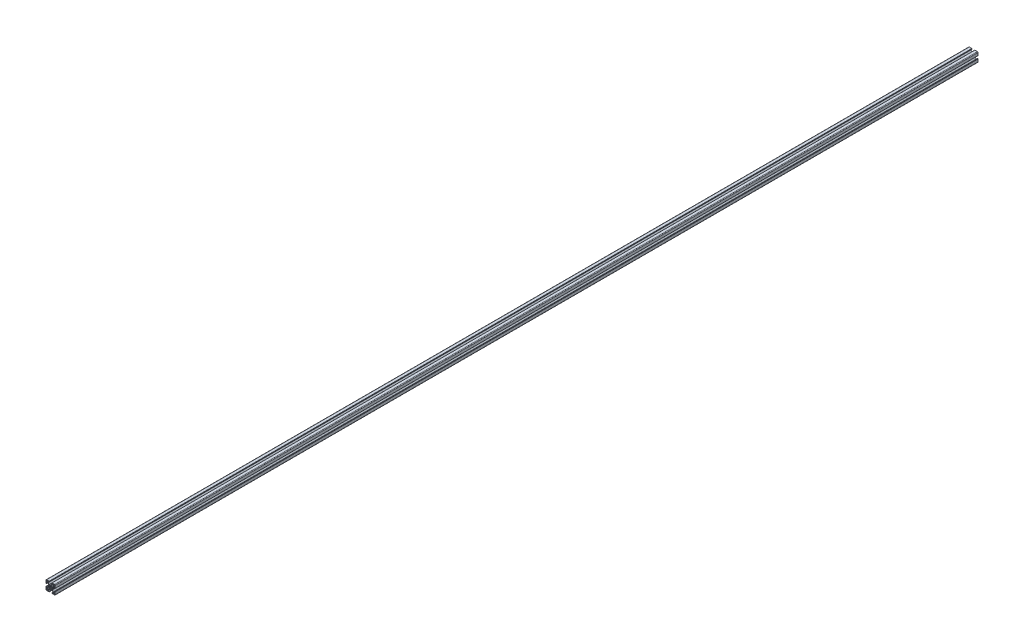
SolidWorks part; units mm, degrees
ref_plane "Płaszczyzna przednia" through (0, 0, 0) normal (0, 0, 1) x (1, 0, 0)
ref_plane "Płaszczyzna górna" through (0, 0, 0) normal (0, 1, 0) x (1, 0, 0)
ref_plane "Płaszczyzna prawa" through (0, 0, 0) normal (1, 0, 0) x (0, 0, -1)
sketch "Sketch1" plane through (0, 0, 0) normal (0, 0, 1) x (1, 0, 0)
  line L0 (109.26, 48.76) -> (107.06, 48.76)
  line L1 (106.06, 47.76) -> (106.06, 45.56)
  line L2 (107.06, 44.56) -> (109.26, 44.56)
  line L3 (110.26, 45.56) -> (110.26, 47.76)
  line L4 (94.9599, 38.3406) -> (93.4241, 39.5784)
  line L5 (92.0547, 38.2147) -> (93.2794, 36.6601)
  line L6 (93.2794, 33.4599) -> (92.0547, 31.9053)
  line L7 (93.4241, 30.5416) -> (94.9599, 31.7794)
  line L8 (98.1601, 31.7794) -> (99.6959, 30.5416)
  line L9 (101.0653, 31.9053) -> (99.8406, 33.4599)
  line L10 (99.8406, 36.6601) -> (101.0653, 38.2147)
  line L11 (99.6959, 39.5784) -> (98.1601, 38.3406)
  line L12 (83.86, 21.36) -> (86.06, 21.36)
  line L13 (87.06, 22.36) -> (87.06, 24.56)
  line L14 (86.06, 25.56) -> (83.86, 25.56)
  line L15 (82.86, 24.56) -> (82.86, 22.36)
  line L16 (110.26, 22.36) -> (110.26, 24.56)
  line L17 (109.26, 25.56) -> (107.06, 25.56)
  line L18 (106.06, 24.56) -> (106.06, 22.36)
  line L19 (86.06, 48.76) -> (83.86, 48.76)
  line L20 (82.86, 47.76) -> (82.86, 45.56)
  line L21 (83.86, 44.56) -> (86.06, 44.56)
  line L22 (87.06, 45.56) -> (87.06, 47.76)
  line L23 (107.06, 21.36) -> (109.26, 21.36)
  line L24 (96.56, 29.5751) -> (97.46, 29.06)
  line L25 (97.46, 29.06) -> (100.7645, 29.06)
  line L26 (100.7645, 29.06) -> (104.81, 25.01)
  line L27 (104.81, 25.01) -> (104.81, 22.46)
  line L28 (104.61, 22.26) -> (101.21, 22.26)
  line L29 (100.61, 21.66) -> (100.61, 20.76)
  line L30 (100.81, 20.56) -> (100.91, 20.56)
  line L31 (101.11, 20.36) -> (101.11, 20.26)
  line L32 (101.31, 20.06) -> (109.56, 20.06)
  line L33 (111.56, 22.06) -> (111.56, 30.31)
  line L34 (111.36, 30.51) -> (111.26, 30.51)
  line L35 (111.06, 30.71) -> (111.06, 30.81)
  line L36 (110.86, 31.01) -> (109.96, 31.01)
  line L37 (109.36, 30.41) -> (109.36, 27.01)
  line L38 (109.16, 26.81) -> (106.61, 26.81)
  line L39 (106.61, 26.81) -> (102.5645, 30.8555)
  line L40 (102.5645, 30.8555) -> (102.5645, 34.16)
  line L41 (102.5645, 34.16) -> (102.0449, 35.06)
  line L42 (102.0449, 35.06) -> (102.5645, 35.96)
  line L43 (102.5645, 35.96) -> (102.5645, 39.2645)
  line L44 (102.5645, 39.2645) -> (106.61, 43.31)
  line L45 (106.61, 43.31) -> (109.16, 43.31)
  line L46 (109.36, 43.11) -> (109.36, 39.71)
  line L47 (109.96, 39.11) -> (110.86, 39.11)
  line L48 (111.06, 39.31) -> (111.06, 39.41)
  line L49 (111.26, 39.61) -> (111.36, 39.61)
  line L50 (111.56, 39.81) -> (111.56, 48.06)
  line L51 (109.56, 50.06) -> (101.31, 50.06)
  line L52 (101.11, 49.86) -> (101.11, 49.76)
  line L53 (100.91, 49.56) -> (100.81, 49.56)
  line L54 (100.61, 49.36) -> (100.61, 48.46)
  line L55 (101.21, 47.86) -> (104.61, 47.86)
  line L56 (104.81, 47.66) -> (104.81, 45.11)
  line L57 (104.81, 45.11) -> (100.7645, 41.06)
  line L58 (100.7645, 41.06) -> (97.46, 41.06)
  line L59 (97.46, 41.06) -> (96.56, 40.5449)
  line L60 (96.56, 40.5449) -> (95.66, 41.06)
  line L61 (95.66, 41.06) -> (92.3555, 41.06)
  line L62 (92.3555, 41.06) -> (88.31, 45.11)
  line L63 (88.31, 45.11) -> (88.31, 47.66)
  line L64 (88.51, 47.86) -> (91.91, 47.86)
  line L65 (92.51, 48.46) -> (92.51, 49.36)
  line L66 (92.31, 49.56) -> (92.21, 49.56)
  line L67 (92.01, 49.76) -> (92.01, 49.86)
  line L68 (91.81, 50.06) -> (83.56, 50.06)
  line L69 (81.56, 48.06) -> (81.56, 39.81)
  line L70 (81.76, 39.61) -> (81.86, 39.61)
  line L71 (82.06, 39.41) -> (82.06, 39.31)
  line L72 (82.26, 39.11) -> (83.16, 39.11)
  line L73 (83.76, 39.71) -> (83.76, 43.11)
  line L74 (83.96, 43.31) -> (86.51, 43.31)
  line L75 (86.51, 43.31) -> (90.5555, 39.2645)
  line L76 (90.5555, 39.2645) -> (90.5555, 35.96)
  line L77 (90.5555, 35.96) -> (91.0751, 35.06)
  line L78 (91.0751, 35.06) -> (90.5555, 34.16)
  line L79 (90.5555, 34.16) -> (90.5555, 30.8555)
  line L80 (90.5555, 30.8555) -> (86.51, 26.81)
  line L81 (86.51, 26.81) -> (83.96, 26.81)
  line L82 (83.76, 27.01) -> (83.76, 30.41)
  line L83 (83.16, 31.01) -> (82.26, 31.01)
  line L84 (82.06, 30.81) -> (82.06, 30.71)
  line L85 (81.86, 30.51) -> (81.76, 30.51)
  line L86 (81.56, 30.31) -> (81.56, 22.06)
  line L87 (83.56, 20.06) -> (91.81, 20.06)
  line L88 (92.01, 20.26) -> (92.01, 20.36)
  line L89 (92.21, 20.56) -> (92.31, 20.56)
  line L90 (92.51, 20.76) -> (92.51, 21.66)
  line L91 (91.91, 22.26) -> (88.51, 22.26)
  line L92 (88.31, 22.46) -> (88.31, 25.01)
  line L93 (88.31, 25.01) -> (92.3555, 29.06)
  line L94 (92.3555, 29.06) -> (95.66, 29.06)
  line L95 (95.66, 29.06) -> (96.56, 29.5751)
  arc A0 (107.06, 48.76) -> (106.06, 47.76) centre (107.06, 47.76) ccw
  arc A1 (106.06, 45.56) -> (107.06, 44.56) centre (107.06, 45.56) ccw
  arc A2 (109.26, 44.56) -> (110.26, 45.56) centre (109.26, 45.56) ccw
  arc A3 (110.26, 47.76) -> (109.26, 48.76) centre (109.26, 47.76) ccw
  arc A4 (93.4241, 39.5784) -> (92.0547, 38.2147) centre (96.56, 35.06) ccw
  arc A5 (93.2794, 36.6601) -> (93.2794, 33.4599) centre (96.56, 35.06) ccw
  arc A6 (92.0547, 31.9053) -> (93.4241, 30.5416) centre (96.56, 35.06) ccw
  arc A7 (94.9599, 31.7794) -> (98.1601, 31.7794) centre (96.56, 35.06) ccw
  arc A8 (99.6959, 30.5416) -> (101.0653, 31.9053) centre (96.56, 35.06) ccw
  arc A9 (99.8406, 33.4599) -> (99.8406, 36.6601) centre (96.56, 35.06) ccw
  arc A10 (101.0653, 38.2147) -> (99.6959, 39.5784) centre (96.56, 35.06) ccw
  arc A11 (98.1601, 38.3406) -> (94.9599, 38.3406) centre (96.56, 35.06) ccw
  arc A12 (86.06, 21.36) -> (87.06, 22.36) centre (86.06, 22.36) ccw
  arc A13 (87.06, 24.56) -> (86.06, 25.56) centre (86.06, 24.56) ccw
  arc A14 (83.86, 25.56) -> (82.86, 24.56) centre (83.86, 24.56) ccw
  arc A15 (82.86, 22.36) -> (83.86, 21.36) centre (83.86, 22.36) ccw
  arc A16 (109.26, 21.36) -> (110.26, 22.36) centre (109.26, 22.36) ccw
  arc A17 (110.26, 24.56) -> (109.26, 25.56) centre (109.26, 24.56) ccw
  arc A18 (107.06, 25.56) -> (106.06, 24.56) centre (107.06, 24.56) ccw
  arc A19 (106.06, 22.36) -> (107.06, 21.36) centre (107.06, 22.36) ccw
  arc A20 (83.86, 48.76) -> (82.86, 47.76) centre (83.86, 47.76) ccw
  arc A21 (82.86, 45.56) -> (83.86, 44.56) centre (83.86, 45.56) ccw
  arc A22 (86.06, 44.56) -> (87.06, 45.56) centre (86.06, 45.56) ccw
  arc A23 (87.06, 47.76) -> (86.06, 48.76) centre (86.06, 47.76) ccw
  arc A24 (104.61, 22.26) -> (104.81, 22.46) centre (104.61, 22.46) ccw
  arc A25 (101.21, 22.26) -> (100.61, 21.66) centre (101.21, 21.66) ccw
  arc A26 (100.61, 20.76) -> (100.81, 20.56) centre (100.81, 20.76) ccw
  arc A27 (101.11, 20.36) -> (100.91, 20.56) centre (100.91, 20.36) ccw
  arc A28 (101.11, 20.26) -> (101.31, 20.06) centre (101.31, 20.26) ccw
  arc A29 (109.56, 20.06) -> (111.56, 22.06) centre (109.56, 22.06) ccw
  arc A30 (111.56, 30.31) -> (111.36, 30.51) centre (111.36, 30.31) ccw
  arc A31 (111.06, 30.71) -> (111.26, 30.51) centre (111.26, 30.71) ccw
  arc A32 (111.06, 30.81) -> (110.86, 31.01) centre (110.86, 30.81) ccw
  arc A33 (109.96, 31.01) -> (109.36, 30.41) centre (109.96, 30.41) ccw
  arc A34 (109.16, 26.81) -> (109.36, 27.01) centre (109.16, 27.01) ccw
  arc A35 (109.36, 43.11) -> (109.16, 43.31) centre (109.16, 43.11) ccw
  arc A36 (109.36, 39.71) -> (109.96, 39.11) centre (109.96, 39.71) ccw
  arc A37 (110.86, 39.11) -> (111.06, 39.31) centre (110.86, 39.31) ccw
  arc A38 (111.26, 39.61) -> (111.06, 39.41) centre (111.26, 39.41) ccw
  arc A39 (111.36, 39.61) -> (111.56, 39.81) centre (111.36, 39.81) ccw
  arc A40 (111.56, 48.06) -> (109.56, 50.06) centre (109.56, 48.06) ccw
  arc A41 (101.31, 50.06) -> (101.11, 49.86) centre (101.31, 49.86) ccw
  arc A42 (100.91, 49.56) -> (101.11, 49.76) centre (100.91, 49.76) ccw
  arc A43 (100.81, 49.56) -> (100.61, 49.36) centre (100.81, 49.36) ccw
  arc A44 (100.61, 48.46) -> (101.21, 47.86) centre (101.21, 48.46) ccw
  arc A45 (104.81, 47.66) -> (104.61, 47.86) centre (104.61, 47.66) ccw
  arc A46 (88.51, 47.86) -> (88.31, 47.66) centre (88.51, 47.66) ccw
  arc A47 (91.91, 47.86) -> (92.51, 48.46) centre (91.91, 48.46) ccw
  arc A48 (92.51, 49.36) -> (92.31, 49.56) centre (92.31, 49.36) ccw
  arc A49 (92.01, 49.76) -> (92.21, 49.56) centre (92.21, 49.76) ccw
  arc A50 (92.01, 49.86) -> (91.81, 50.06) centre (91.81, 49.86) ccw
  arc A51 (83.56, 50.06) -> (81.56, 48.06) centre (83.56, 48.06) ccw
  arc A52 (81.56, 39.81) -> (81.76, 39.61) centre (81.76, 39.81) ccw
  arc A53 (82.06, 39.41) -> (81.86, 39.61) centre (81.86, 39.41) ccw
  arc A54 (82.06, 39.31) -> (82.26, 39.11) centre (82.26, 39.31) ccw
  arc A55 (83.16, 39.11) -> (83.76, 39.71) centre (83.16, 39.71) ccw
  arc A56 (83.96, 43.31) -> (83.76, 43.11) centre (83.96, 43.11) ccw
  arc A57 (83.76, 27.01) -> (83.96, 26.81) centre (83.96, 27.01) ccw
  arc A58 (83.76, 30.41) -> (83.16, 31.01) centre (83.16, 30.41) ccw
  arc A59 (82.26, 31.01) -> (82.06, 30.81) centre (82.26, 30.81) ccw
  arc A60 (81.86, 30.51) -> (82.06, 30.71) centre (81.86, 30.71) ccw
  arc A61 (81.76, 30.51) -> (81.56, 30.31) centre (81.76, 30.31) ccw
  arc A62 (81.56, 22.06) -> (83.56, 20.06) centre (83.56, 22.06) ccw
  arc A63 (91.81, 20.06) -> (92.01, 20.26) centre (91.81, 20.26) ccw
  arc A64 (92.21, 20.56) -> (92.01, 20.36) centre (92.21, 20.36) ccw
  arc A65 (92.31, 20.56) -> (92.51, 20.76) centre (92.31, 20.76) ccw
  arc A66 (92.51, 21.66) -> (91.91, 22.26) centre (91.91, 21.66) ccw
  arc A67 (88.31, 22.46) -> (88.51, 22.26) centre (88.51, 22.46) ccw
  dimension "D1" = 3.65
  dimension "D2" = 30
  dimension "D3" = 30
  dimension "D4" = 8.1
extrude "Sigma Profile" add sketch "Sketch1" along normal blind 3000
